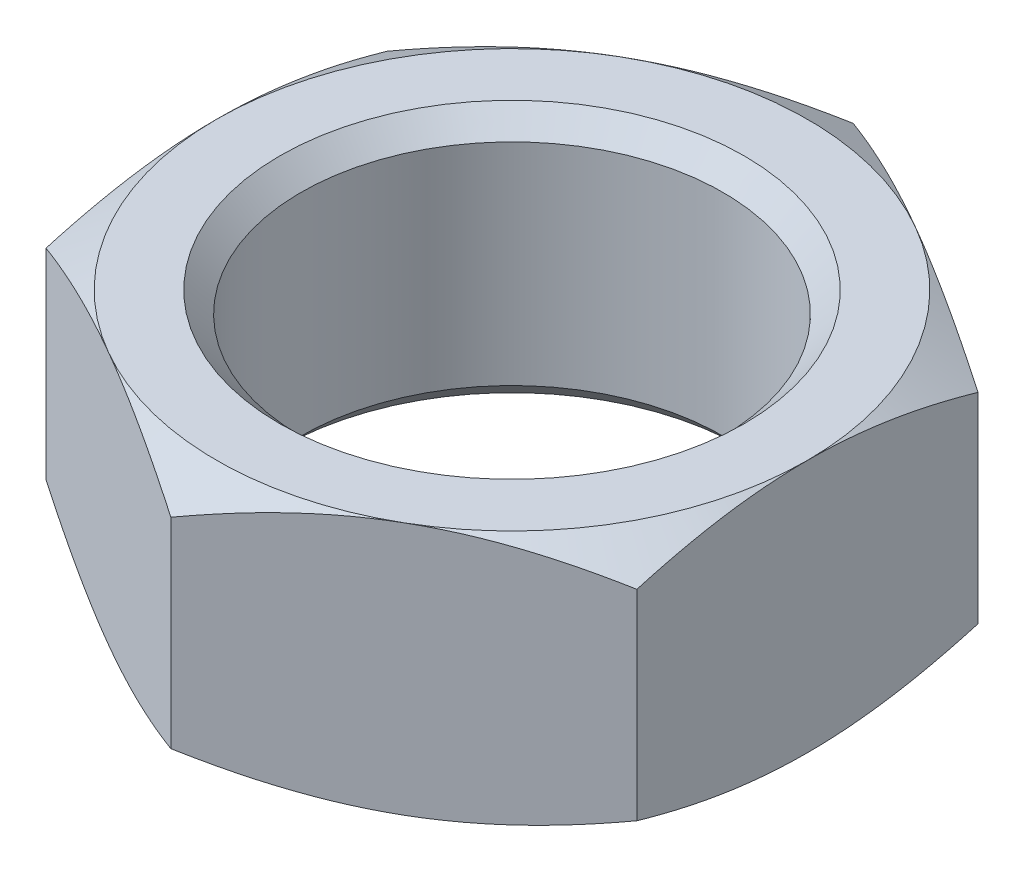
SolidWorks part; units mm, degrees
ref_plane "Front Plane" through (0, 0, 0) normal (0, 0, 1) x (1, 0, 0)
ref_plane "Top Plane" through (0, 0, 0) normal (0, 1, 0) x (1, 0, 0)
ref_plane "Right Plane" through (0, 0, 0) normal (1, 0, 0) x (0, 0, -1)
sketch "Sketch1" plane through (0, 0, 0) normal (0, 1, 0) x (1, 0, 0)
  line L1 (14, 8.0829) -> (0, 16.1658)
  line L2 (0, 16.1658) -> (-14, 8.0829)
  line L3 (-14, 8.0829) -> (-14, -8.0829)
  line L4 (-14, -8.0829) -> (0, -16.1658)
  line L5 (0, -16.1658) -> (14, -8.0829)
  line L6 (14, -8.0829) -> (14, 8.0829)
  circle A0 centre (0, 0) radius 14 construction
  dimension "D1" = 28
extrude "Boss-Extrude1" add sketch "Sketch1" along normal mid plane 12
sketch "Sketch2" plane through (0, 6, 0) normal (0, 1, 0) x (1, 0, 0)
  line L0 (14, 8.0829) -> (0, 16.1658) construction
  circle A0 centre (0, 0) radius 14
extrude "Cut-Extrude1" cut sketch "Sketch2" against normal blind 12 draft 60 flip side to cut
mirror "Mirror1" about plane through (0, 0, 0) normal (0, 1, 0) of "Cut-Extrude1"
sketch "Sketch3" plane through (0, 6, 0) normal (0, 1, 0) x (1, 0, 0)
  circle A0 centre (0, 0) radius 10
  dimension "D1" = 20
extrude "Cut-Extrude2" cut sketch "Sketch3" against normal through all
chamfer "Chamfer1" distance 1 angle 45 2 edges at (0, -6, 10) (0, 6, 10)
